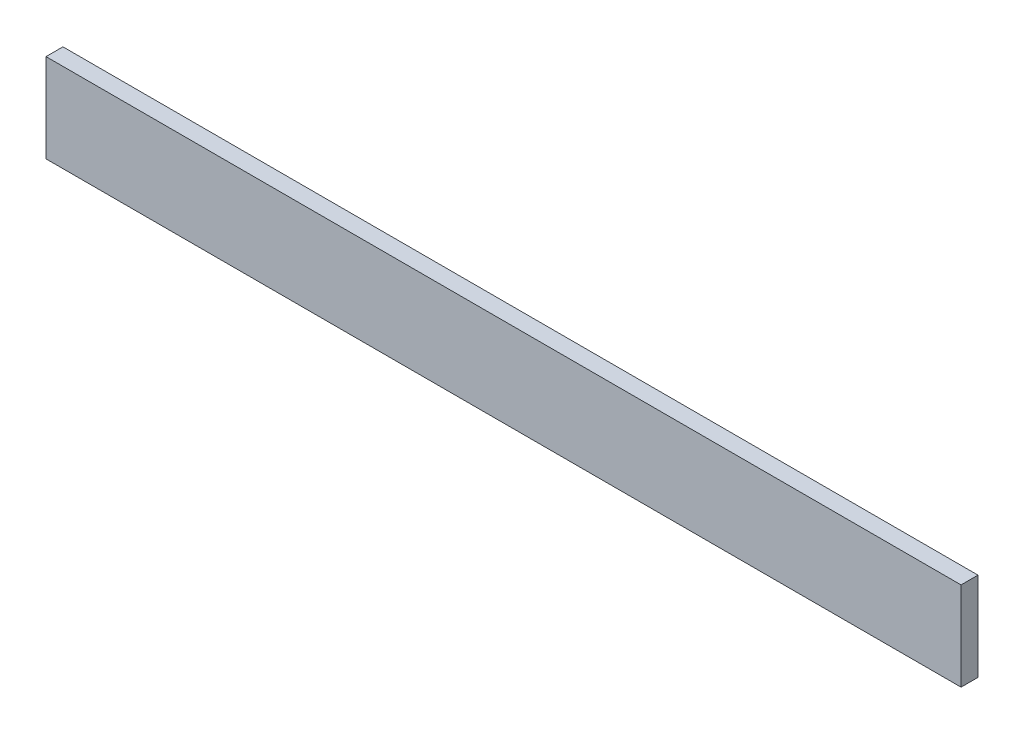
SolidWorks part; units mm, degrees
ref_plane "Front Plane" through (0, 0, 0) normal (0, 0, 1) x (1, 0, 0)
ref_plane "Top Plane" through (0, 0, 0) normal (0, 1, 0) x (1, 0, 0)
ref_plane "Right Plane" through (0, 0, 0) normal (1, 0, 0) x (0, 0, -1)
sketch "Model" plane through (0, 0, 0) normal (0, 0, 1) x (1, 0, 0)
  line L0 (9.5075, 23.7112) -> (9.5075, 8.0285)
  line L1 (9.5075, 8.0285) -> (171.5075, 8.0285)
  line L2 (171.5075, 8.0285) -> (171.5075, 23.7112)
  line L3 (171.5075, 23.7112) -> (9.5075, 23.7112)
extrude "Boss-Extrude1" add sketch "Model" along normal blind 3 contours L0 L1 L2 L3
